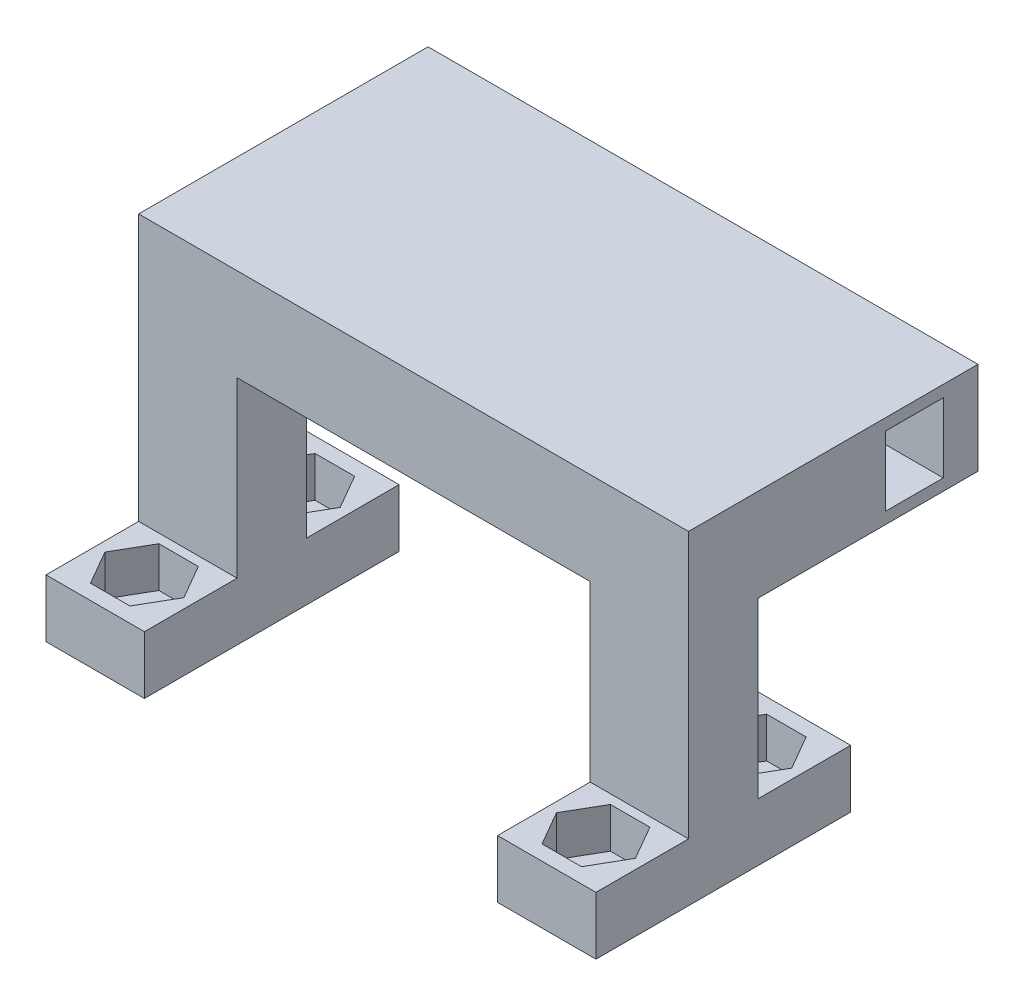
SolidWorks part; units mm, degrees
ref_plane "Front Plane" through (0, 0, 0) normal (0, 0, 1) x (1, 0, 0)
ref_plane "Top Plane" through (0, 0, 0) normal (0, 1, 0) x (1, 0, 0)
ref_plane "Right Plane" through (0, 0, 0) normal (1, 0, 0) x (0, 0, -1)
sketch "Sketch1" plane through (0, 0, 0) normal (0, 1, 0) x (1, 0, 0)
  line L1 (-4.25, -11) -> (4.25, -11)
  line L2 (-4.25, -11) -> (-4.25, 11)
  line L3 (-4.25, 11) -> (4.25, 11)
  line L4 (4.25, -11) -> (4.25, 11)
  line L5 (-4.25, -11) -> (4.25, 11) construction
  line L6 (-4.25, 11) -> (4.25, -11) construction
  point P0 (0, 0)
  dimension "D1" = 22
  dimension "D2" = 8.5
extrude "Boss-Extrude1" add sketch "Sketch1" along normal blind 5
sketch "Sketch2" plane through (0, 5, 0) normal (0, 1, 0) x (1, 0, 0)
  line L0 (-4.25, 2.5) -> (4.25, 2.5) construction
  line L1 (-4.25, 11) -> (-4.25, -11) construction
  line L2 (4.25, -11) -> (4.25, 11) construction
  line L3 (-4.25, -2.5) -> (4.25, -2.5) construction
  line L4 (4.25, 11) -> (-4.25, 11) construction
  line L5 (-4.25, -11) -> (4.25, -11) construction
  line L6 (0, 0) -> (1.3647, 0) construction
  line L7 (-1.705, 9.7031) -> (-3.41, 6.75)
  line L8 (-3.41, 6.75) -> (-1.705, 3.7969)
  line L9 (-1.705, 3.7969) -> (1.705, 3.7969)
  line L10 (1.705, 3.7969) -> (3.41, 6.75)
  line L11 (3.41, 6.75) -> (1.705, 9.7031)
  line L12 (1.705, 9.7031) -> (-1.705, 9.7031)
  line L13 (1.705, -9.7031) -> (-1.705, -9.7031)
  line L14 (3.41, -6.75) -> (1.705, -9.7031)
  line L15 (1.705, -3.7969) -> (3.41, -6.75)
  line L16 (-1.705, -3.7969) -> (1.705, -3.7969)
  line L17 (-3.41, -6.75) -> (-1.705, -3.7969)
  line L18 (-1.705, -9.7031) -> (-3.41, -6.75)
  circle A0 centre (0, 6.75) radius 2.9531 construction
  point P8 (0, 6.75)
  point P12 (0, -6.75)
  dimension "D1" = 2.5
  dimension "D2" = 4.25
  dimension "2.5" = 2.5
  dimension "D3" = 4.25
  dimension "D4" = 3.41
extrude "Cut-Extrude1" cut sketch "Sketch2" against normal blind 3.5
sketch "Sketch3" plane through (0, 1.5, 0) normal (0, 1, 0) x (1, 0, 0)
  line L0 (3.41, 6.75) -> (-3.41, 6.75) construction
  line L1 (3.41, -6.75) -> (-3.41, -6.75) construction
  circle A0 centre (0, 6.75) radius 1.5
  circle A1 centre (0, -6.75) radius 1.5
  circle A2 centre (39, 6.75) radius 1.5
  circle A3 centre (39, -6.75) radius 1.5
  point P16 (0, 0)
  dimension "D1" = 3
  dimension "D2" = 3
  dimension "D3" = 3
  dimension "D5" = 3
  dimension "D4" = 39
extrude "Cut-Extrude2" cut sketch "Sketch3" against normal blind 1.5
sketch "Sketch4" plane through (0, 5, 0) normal (0, 1, 0) x (1, 0, 0)
  line L0 (4.25, -11) -> (4.25, 11) construction
  line L1 (-4.25, -3) -> (4.25, -3)
  line L2 (-4.25, -3) -> (-4.25, 3)
  line L3 (-4.25, 3) -> (4.25, 3)
  line L4 (4.25, -3) -> (4.25, 3)
  line L5 (-4.25, -3) -> (4.25, 3) construction
  line L6 (-4.25, 3) -> (4.25, -3) construction
  point P0 (0, 0)
  dimension "D1" = 6
extrude "Boss-Extrude2" add sketch "Sketch4" along normal blind 23
sketch "Sketch7" plane through (0, 0, 0) normal (0, 1, 0) x (1, 0, 0)
  line L1 (34.75, -11) -> (43.25, -11)
  line L2 (34.75, -11) -> (34.75, 11)
  line L3 (34.75, 11) -> (43.25, 11)
  line L4 (43.25, -11) -> (43.25, 11)
  line L5 (34.75, -11) -> (43.25, 11) construction
  line L6 (34.75, 11) -> (43.25, -11) construction
  point P0 (39, 0)
  point P2 (39, 0)
  dimension "D1" = 22
  dimension "D2" = 8.5
extrude "Boss-Extrude4" add sketch "Sketch7" along normal blind 5 separate body
sketch "Sketch8" plane through (0, 5, 0) normal (0, 1, 0) x (1, 0, 0)
  line L0 (43.25, 11) -> (34.75, 11) construction
  line L1 (40.705, 9.7031) -> (37.295, 9.7031)
  line L2 (37.295, 9.7031) -> (35.59, 6.75)
  line L3 (35.59, 6.75) -> (37.295, 3.7969)
  line L4 (37.295, 3.7969) -> (40.705, 3.7969)
  line L5 (40.705, 3.7969) -> (42.41, 6.75)
  line L6 (42.41, 6.75) -> (40.705, 9.7031)
  line L7 (40.705, -3.7969) -> (37.295, -3.7969)
  line L8 (37.295, -3.7969) -> (35.59, -6.75)
  line L9 (35.59, -6.75) -> (37.295, -9.7031)
  line L10 (37.295, -9.7031) -> (40.705, -9.7031)
  line L11 (40.705, -9.7031) -> (42.41, -6.75)
  line L12 (42.41, -6.75) -> (40.705, -3.7969)
  line L13 (34.75, -11) -> (43.25, -11) construction
  circle A0 centre (39, 6.75) radius 2.9531 construction
  circle A1 centre (39, -6.75) radius 2.9531 construction
  point P0 (39, 6.75)
  point P1 (39, -6.75)
  dimension "D1" = 3.41
  dimension "D2" = 3.41
extrude "Cut-Extrude3" cut sketch "Sketch8" against normal blind 3.5
sketch "Sketch9" plane through (0, 1.5, 0) normal (0, 1, 0) x (1, 0, 0)
  circle A0 centre (39, 6.75) radius 1.5
  circle A1 centre (39, -6.75) radius 1.5
extrude "Cut-Extrude4" cut sketch "Sketch9" against normal blind 3.5
sketch "Sketch10" plane through (0, 5, 0) normal (0, 1, 0) x (1, 0, 0)
  line L0 (34.75, 11) -> (34.75, -11) construction
  line L2 (43.25, 3) -> (34.75, 3)
  line L3 (43.25, 3) -> (43.25, -3)
  line L4 (43.25, -3) -> (34.75, -3)
  line L5 (34.75, 3) -> (34.75, -3)
  line L6 (43.25, 3) -> (34.75, -3) construction
  line L7 (43.25, -3) -> (34.75, 3) construction
  point P0 (39, 0)
  point P1 (34.75, -3)
  point P2 (39, 0)
  dimension "D1" = 3
extrude "Boss-Extrude5" add sketch "Sketch10" along normal up to surface (23 mm away) up to face at (0, 28, 0)
sketch "Sketch6" plane through (4.25, 0, 0) normal (1, 0, 0) x (0, 0, -1)
  line L0 (3, 28) -> (3, 5) construction
  line L1 (-3, 28) -> (3, 28)
  line L2 (-3, 28) -> (-3, 20)
  line L3 (-3, 20) -> (3, 20)
  line L4 (3, 28) -> (3, 20)
  dimension "D1" = 8
extrude "Boss-Extrude6" add sketch "Sketch6" along normal up to surface (30.5 mm away) up to face at (34.75, 9.5, 0)
sketch "Sketch11" plane through (0, 0, -3) normal (0, 0, -1) x (-1, 0, 0)
  line L0 (4.25, 28) -> (4.25, 5) construction
  line L1 (-43.25, 28) -> (4.25, 28)
  line L2 (-43.25, 28) -> (-43.25, 20)
  line L3 (-43.25, 20) -> (4.25, 20)
  line L4 (4.25, 28) -> (4.25, 20)
extrude "Boss-Extrude7" add sketch "Sketch11" along normal blind 13.5
sketch "Sketch12" plane through (0, 0, -16.5) normal (0, 0, -1) x (-1, 0, 0)
  line L1 (-43.25, 28) -> (4.25, 28)
  line L2 (-43.25, 28) -> (-43.25, 20)
  line L3 (-43.25, 20) -> (4.25, 20)
  line L4 (4.25, 28) -> (4.25, 20)
extrude "Boss-Extrude8" add sketch "Sketch12" along normal blind 5.5
sketch "Sketch13" plane through (-4.25, 0, 0) normal (-1, 0, 0) x (0, 0, 1)
  line L0 (-22, 20) -> (-22, 28) construction
  line L1 (-19, 21) -> (-14, 21)
  line L2 (-19, 21) -> (-19, 27)
  line L3 (-19, 27) -> (-14, 27)
  line L4 (-14, 21) -> (-14, 27)
  line L5 (-19, 21) -> (-14, 27) construction
  line L6 (-19, 27) -> (-14, 21) construction
  line L7 (-22, 20) -> (-3, 20) construction
  point P0 (-16.5, 24)
  dimension "D1" = 6
  dimension "D2" = 5
  dimension "D3" = 3
  dimension "D4" = 1
extrude "Cut-Extrude5" cut sketch "Sketch13" against normal blind 15
sketch "Sketch14" plane through (0, 0, -22) normal (0, 0, -1) x (-1, 0, 0)
  line L0 (-10.75, 28) -> (-10.75, 20) construction
  line L1 (4.25, 28) -> (-43.25, 28) construction
  line L2 (-43.25, 20) -> (4.25, 20) construction
  line L3 (4.25, 20) -> (4.25, 28) construction
  line L4 (-43.25, 24) -> (4.25, 24) construction
  line L5 (-43.25, 28) -> (-43.25, 20) construction
  line L7 (-10.75, 21) -> (-5.75, 21)
  line L8 (-10.75, 21) -> (-10.75, 27)
  line L9 (-10.75, 27) -> (-5.75, 27)
  line L10 (-5.75, 21) -> (-5.75, 27)
  line L11 (-10.75, 21) -> (-5.75, 27) construction
  line L12 (-10.75, 27) -> (-5.75, 21) construction
  point P12 (-8.25, 24)
  dimension "D1" = 15
  dimension "D2" = 5
  dimension "D3" = 6
  dimension "D4" = 0
extrude "Cut-Extrude6" cut sketch "Sketch14" against normal blind 4
sketch "Sketch15" plane through (43.25, 0, 0) normal (1, 0, 0) x (0, 0, -1)
  line L0 (22, 24) -> (-3, 24) construction
  line L1 (22, 28) -> (22, 20) construction
  line L2 (-3, 28) -> (-3, 5) construction
  line L4 (14, 21) -> (19, 21)
  line L5 (14, 21) -> (14, 27)
  line L6 (14, 27) -> (19, 27)
  line L7 (19, 21) -> (19, 27)
  line L8 (14, 21) -> (19, 27) construction
  line L9 (14, 27) -> (19, 21) construction
  point P6 (16.5, 24)
  dimension "D1" = 6
  dimension "D2" = 5
  dimension "D3" = 3
extrude "Cut-Extrude7" cut sketch "Sketch15" against normal blind 15
sketch "Sketch16" plane through (0, 0, -22) normal (0, 0, -1) x (-1, 0, 0)
  line L0 (-43.25, 24) -> (4.25, 24) construction
  line L1 (-43.25, 28) -> (-43.25, 20) construction
  line L2 (4.25, 20) -> (4.25, 28) construction
  line L3 (-28.25, 20) -> (-28.25, 28) construction
  line L4 (-33.25, 21) -> (-28.25, 21)
  line L5 (-33.25, 21) -> (-33.25, 27)
  line L6 (-33.25, 27) -> (-28.25, 27)
  line L7 (-28.25, 21) -> (-28.25, 27)
  line L8 (-33.25, 21) -> (-28.25, 27) construction
  line L9 (-33.25, 27) -> (-28.25, 21) construction
  line L10 (-43.25, 20) -> (4.25, 20) construction
  line L11 (4.25, 28) -> (-43.25, 28) construction
  point P6 (-30.75, 24)
  dimension "D1" = 15
  dimension "D2" = 0
  dimension "D3" = 5
  dimension "D4" = 6
extrude "Cut-Extrude8" cut sketch "Sketch16" against normal blind 4
